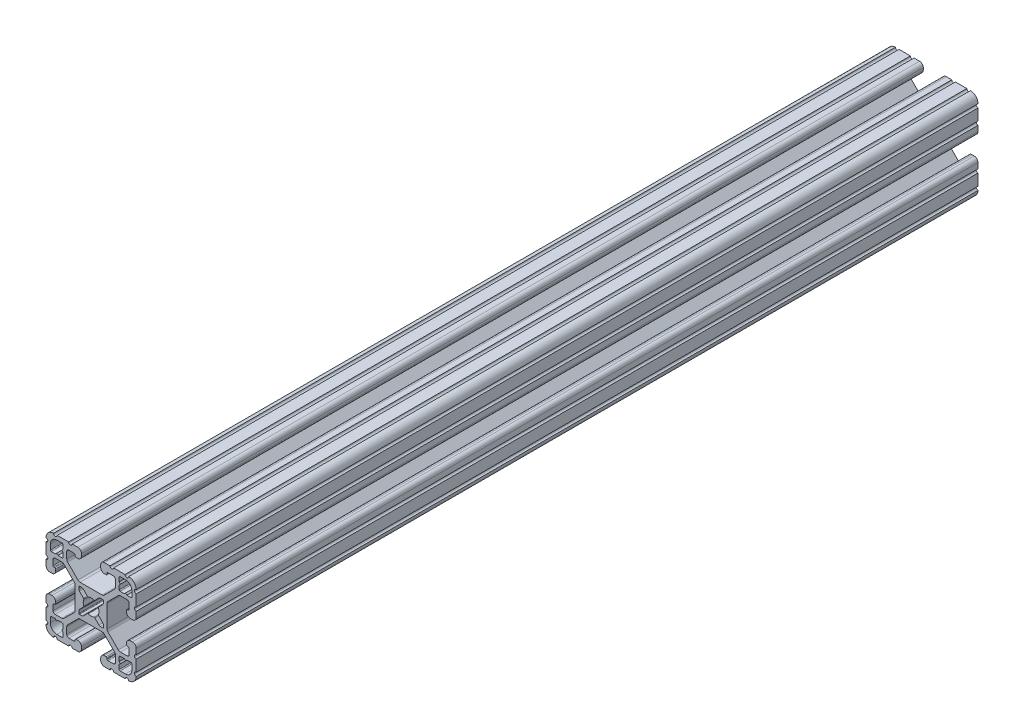
SolidWorks part; units mm, degrees
ref_plane "Front Plane" through (0, 0, 0) normal (0, 0, 1) x (1, 0, 0)
ref_plane "Top Plane" through (0, 0, 0) normal (0, 1, 0) x (1, 0, 0)
ref_plane "Right Plane" through (0, 0, 0) normal (1, 0, 0) x (0, 0, -1)
ref_plane "Plane1" through (0, 0, -2322.576) normal (0, 0, -1) x (-1, 0, 0)
sketch "Sketch1" plane through (0, 0, -2322.576) normal (0, 0, -1) x (-1, 0, 0)
  line L0 (17.2466, 14.4526) -> (17.2466, 12.2428)
  line L1 (16.8656, 11.8618) -> (15.0927, 11.8618)
  line L2 (15.0927, 11.8618) -> (14.5542, 12.4003)
  line L3 (14.5542, 12.4003) -> (14.0157, 11.8618)
  line L4 (14.0157, 11.8618) -> (12.2428, 11.8618)
  line L5 (11.8618, 12.2428) -> (11.8618, 14.0157)
  line L6 (11.8618, 14.0157) -> (12.4003, 14.5542)
  line L7 (12.4003, 14.5542) -> (11.8618, 15.0927)
  line L8 (11.8618, 15.0927) -> (11.8618, 16.8656)
  line L9 (12.2428, 17.2466) -> (14.4526, 17.2466)
  line L10 (17.2466, -12.2428) -> (17.2466, -14.4526)
  line L11 (14.4526, -17.2466) -> (12.2428, -17.2466)
  line L12 (11.8618, -16.8656) -> (11.8618, -15.0927)
  line L13 (11.8618, -15.0927) -> (12.4003, -14.5542)
  line L14 (12.4003, -14.5542) -> (11.8618, -14.0157)
  line L15 (11.8618, -14.0157) -> (11.8618, -12.2428)
  line L16 (12.2428, -11.8618) -> (14.0157, -11.8618)
  line L17 (14.0157, -11.8618) -> (14.5542, -12.4003)
  line L18 (14.5542, -12.4003) -> (15.0927, -11.8618)
  line L19 (15.0927, -11.8618) -> (16.8656, -11.8618)
  line L20 (5.1689, -3.9207) -> (5.1689, -4.9149)
  line L21 (4.9149, -5.1689) -> (3.9207, -5.1689)
  line L22 (3.2921, -4.9085) -> (1.5823, -3.1988)
  line L23 (-1.5823, -3.1988) -> (-3.2921, -4.9085)
  line L24 (-3.9207, -5.1689) -> (-4.9149, -5.1689)
  line L25 (-5.1689, -4.9149) -> (-5.1689, -3.9207)
  line L26 (-4.9085, -3.2921) -> (-3.1988, -1.5823)
  line L27 (-3.1988, 1.5823) -> (-4.9085, 3.2921)
  line L28 (-5.1689, 3.9207) -> (-5.1689, 4.9149)
  line L29 (-4.9149, 5.1689) -> (-3.9207, 5.1689)
  line L30 (-3.2921, 4.9085) -> (-1.5823, 3.1988)
  line L31 (1.5823, 3.1988) -> (3.2921, 4.9085)
  line L32 (3.9207, 5.1689) -> (4.9149, 5.1689)
  line L33 (5.1689, 4.9149) -> (5.1689, 3.9207)
  line L34 (4.9085, 3.2921) -> (3.1988, 1.5823)
  line L35 (3.1988, -1.5823) -> (4.9085, -3.2921)
  line L36 (-11.8618, -12.2428) -> (-11.8618, -14.0157)
  line L37 (-11.8618, -14.0157) -> (-12.4003, -14.5542)
  line L38 (-12.4003, -14.5542) -> (-11.8618, -15.0927)
  line L39 (-11.8618, -15.0927) -> (-11.8618, -16.8656)
  line L40 (-12.2428, -17.2466) -> (-14.4526, -17.2466)
  line L41 (-17.2466, -14.4526) -> (-17.2466, -12.2428)
  line L42 (-16.8656, -11.8618) -> (-15.0927, -11.8618)
  line L43 (-15.0927, -11.8618) -> (-14.5542, -12.4003)
  line L44 (-14.5542, -12.4003) -> (-14.0157, -11.8618)
  line L45 (-14.0157, -11.8618) -> (-12.2428, -11.8618)
  line L46 (-11.8618, 16.8656) -> (-11.8618, 15.0927)
  line L47 (-11.8618, 15.0927) -> (-12.4003, 14.5542)
  line L48 (-12.4003, 14.5542) -> (-11.8618, 14.0157)
  line L49 (-11.8618, 14.0157) -> (-11.8618, 12.2428)
  line L50 (-12.2428, 11.8618) -> (-14.0157, 11.8618)
  line L51 (-14.0157, 11.8618) -> (-14.5542, 12.4003)
  line L52 (-14.5542, 12.4003) -> (-15.0927, 11.8618)
  line L53 (-15.0927, 11.8618) -> (-16.8656, 11.8618)
  line L54 (-17.2466, 12.2428) -> (-17.2466, 14.4526)
  line L55 (-14.4526, 17.2466) -> (-12.2428, 17.2466)
  line L56 (19.05, -14.3256) -> (19.05, -9.4996)
  line L57 (19.05, -7.9756) -> (19.05, -5.6388)
  line L58 (17.4752, -4.064) -> (16.5608, -4.064)
  line L59 (14.986, -5.6388) -> (14.986, -6.35)
  line L60 (15.367, -6.731) -> (15.6972, -6.731)
  line L61 (16.0782, -7.112) -> (16.0782, -9.398)
  line L62 (15.1892, -10.287) -> (12.3756, -10.287)
  line L63 (11.4776, -9.915) -> (7.1157, -5.5531)
  line L64 (6.7437, -4.6551) -> (6.7437, 4.6551)
  line L65 (7.1157, 5.5531) -> (11.4776, 9.915)
  line L66 (12.3756, 10.287) -> (15.1892, 10.287)
  line L67 (16.0782, 9.398) -> (16.0782, 7.112)
  line L68 (15.6972, 6.731) -> (15.367, 6.731)
  line L69 (14.986, 6.35) -> (14.986, 5.6388)
  line L70 (16.5608, 4.064) -> (17.4752, 4.064)
  line L71 (19.05, 5.6388) -> (19.05, 7.9756)
  line L72 (19.05, 9.4996) -> (19.05, 14.3256)
  line L73 (14.3256, 19.05) -> (9.4996, 19.05)
  line L74 (7.9756, 19.05) -> (5.6388, 19.05)
  line L75 (4.064, 17.4752) -> (4.064, 16.5608)
  line L76 (5.6388, 14.986) -> (6.35, 14.986)
  line L77 (6.731, 15.367) -> (6.731, 15.6972)
  line L78 (7.112, 16.0782) -> (9.398, 16.0782)
  line L79 (10.287, 15.1892) -> (10.287, 12.3756)
  line L80 (9.915, 11.4776) -> (5.5531, 7.1157)
  line L81 (4.6551, 6.7437) -> (-4.6551, 6.7437)
  line L82 (-5.5531, 7.1157) -> (-9.915, 11.4776)
  line L83 (-10.287, 12.3756) -> (-10.287, 15.1892)
  line L84 (-9.398, 16.0782) -> (-7.112, 16.0782)
  line L85 (-6.731, 15.6972) -> (-6.731, 15.367)
  line L86 (-6.35, 14.986) -> (-5.6388, 14.986)
  line L87 (-4.064, 16.5608) -> (-4.064, 17.4752)
  line L88 (-5.6388, 19.05) -> (-7.9756, 19.05)
  line L89 (-9.4996, 19.05) -> (-14.3256, 19.05)
  line L90 (-19.05, 14.3256) -> (-19.05, 9.4996)
  line L91 (-19.05, 7.9756) -> (-19.05, 5.6388)
  line L92 (-17.4752, 4.064) -> (-16.5608, 4.064)
  line L93 (-14.986, 5.6388) -> (-14.986, 6.35)
  line L94 (-15.367, 6.731) -> (-15.6972, 6.731)
  line L95 (-16.0782, 7.112) -> (-16.0782, 9.398)
  line L96 (-15.1892, 10.287) -> (-12.3756, 10.287)
  line L97 (-11.4776, 9.915) -> (-7.1157, 5.5531)
  line L98 (-6.7437, 4.6551) -> (-6.7437, -4.6551)
  line L99 (-7.1157, -5.5531) -> (-11.4776, -9.915)
  line L100 (-12.3756, -10.287) -> (-15.1892, -10.287)
  line L101 (-16.0782, -9.398) -> (-16.0782, -7.112)
  line L102 (-15.6972, -6.731) -> (-15.367, -6.731)
  line L103 (-14.986, -6.35) -> (-14.986, -5.6388)
  line L104 (-16.5608, -4.064) -> (-17.4752, -4.064)
  line L105 (-19.05, -5.6388) -> (-19.05, -7.9756)
  line L106 (-19.05, -9.4996) -> (-19.05, -14.3256)
  line L107 (-14.3256, -19.05) -> (-9.4996, -19.05)
  line L108 (-7.9756, -19.05) -> (-5.6388, -19.05)
  line L109 (-4.064, -17.4752) -> (-4.064, -16.5608)
  line L110 (-5.6388, -14.986) -> (-6.35, -14.986)
  line L111 (-6.731, -15.367) -> (-6.731, -15.6972)
  line L112 (-7.112, -16.0782) -> (-9.398, -16.0782)
  line L113 (-10.287, -15.1892) -> (-10.287, -12.3756)
  line L114 (-9.915, -11.4776) -> (-5.5531, -7.1157)
  line L115 (-4.6551, -6.7437) -> (4.6551, -6.7437)
  line L116 (5.5531, -7.1157) -> (9.915, -11.4776)
  line L117 (10.287, -12.3756) -> (10.287, -15.1892)
  line L118 (9.398, -16.0782) -> (7.112, -16.0782)
  line L119 (6.731, -15.6972) -> (6.731, -15.367)
  line L120 (6.35, -14.986) -> (5.6388, -14.986)
  line L121 (4.064, -16.5608) -> (4.064, -17.4752)
  line L122 (5.6388, -19.05) -> (7.9756, -19.05)
  line L123 (9.4996, -19.05) -> (14.3256, -19.05)
  arc A0 (17.2466, 12.2428) -> (16.8656, 11.8618) centre (16.8656, 12.2428) cw
  arc A1 (12.2428, 11.8618) -> (11.8618, 12.2428) centre (12.2428, 12.2428) cw
  arc A2 (11.8618, 16.8656) -> (12.2428, 17.2466) centre (12.2428, 16.8656) cw
  arc A3 (14.4526, 17.2466) -> (17.2466, 14.4526) centre (14.4526, 14.4526) cw
  arc A4 (17.2466, -14.4526) -> (14.4526, -17.2466) centre (14.4526, -14.4526) cw
  arc A5 (12.2428, -17.2466) -> (11.8618, -16.8656) centre (12.2428, -16.8656) cw
  arc A6 (11.8618, -12.2428) -> (12.2428, -11.8618) centre (12.2428, -12.2428) cw
  arc A7 (16.8656, -11.8618) -> (17.2466, -12.2428) centre (16.8656, -12.2428) cw
  arc A8 (5.1689, -4.9149) -> (4.9149, -5.1689) centre (4.9149, -4.9149) cw
  arc A9 (3.9207, -5.1689) -> (3.2921, -4.9085) centre (3.9207, -4.2799) cw
  arc A10 (1.5823, -3.1988) -> (1.178, -3.1119) centre (1.3129, -3.4682) ccw
  arc A11 (1.178, -3.1119) -> (-1.178, -3.1119) centre (0, 0) cw
  arc A12 (-1.178, -3.1119) -> (-1.5823, -3.1988) centre (-1.3129, -3.4682) ccw
  arc A13 (-3.2921, -4.9085) -> (-3.9207, -5.1689) centre (-3.9207, -4.2799) cw
  arc A14 (-4.9149, -5.1689) -> (-5.1689, -4.9149) centre (-4.9149, -4.9149) cw
  arc A15 (-5.1689, -3.9207) -> (-4.9085, -3.2921) centre (-4.2799, -3.9207) cw
  arc A16 (-3.1988, -1.5823) -> (-3.1119, -1.178) centre (-3.4682, -1.3129) ccw
  arc A17 (-3.1119, -1.178) -> (-3.1119, 1.178) centre (0, 0) cw
  arc A18 (-3.1119, 1.178) -> (-3.1988, 1.5823) centre (-3.4682, 1.3129) ccw
  arc A19 (-4.9085, 3.2921) -> (-5.1689, 3.9207) centre (-4.2799, 3.9207) cw
  arc A20 (-5.1689, 4.9149) -> (-4.9149, 5.1689) centre (-4.9149, 4.9149) cw
  arc A21 (-3.9207, 5.1689) -> (-3.2921, 4.9085) centre (-3.9207, 4.2799) cw
  arc A22 (-1.5823, 3.1988) -> (-1.178, 3.1119) centre (-1.3129, 3.4682) ccw
  arc A23 (-1.178, 3.1119) -> (1.178, 3.1119) centre (0, 0) cw
  arc A24 (1.178, 3.1119) -> (1.5823, 3.1988) centre (1.3129, 3.4682) ccw
  arc A25 (3.2921, 4.9085) -> (3.9207, 5.1689) centre (3.9207, 4.2799) cw
  arc A26 (4.9149, 5.1689) -> (5.1689, 4.9149) centre (4.9149, 4.9149) cw
  arc A27 (5.1689, 3.9207) -> (4.9085, 3.2921) centre (4.2799, 3.9207) cw
  arc A28 (3.1988, 1.5823) -> (3.1119, 1.178) centre (3.4682, 1.3129) ccw
  arc A29 (3.1119, 1.178) -> (3.1119, -1.178) centre (0, 0) cw
  arc A30 (3.1119, -1.178) -> (3.1988, -1.5823) centre (3.4682, -1.3129) ccw
  arc A31 (4.9085, -3.2921) -> (5.1689, -3.9207) centre (4.2799, -3.9207) cw
  arc A32 (-11.8618, -16.8656) -> (-12.2428, -17.2466) centre (-12.2428, -16.8656) cw
  arc A33 (-14.4526, -17.2466) -> (-17.2466, -14.4526) centre (-14.4526, -14.4526) cw
  arc A34 (-17.2466, -12.2428) -> (-16.8656, -11.8618) centre (-16.8656, -12.2428) cw
  arc A35 (-12.2428, -11.8618) -> (-11.8618, -12.2428) centre (-12.2428, -12.2428) cw
  arc A36 (-12.2428, 17.2466) -> (-11.8618, 16.8656) centre (-12.2428, 16.8656) cw
  arc A37 (-11.8618, 12.2428) -> (-12.2428, 11.8618) centre (-12.2428, 12.2428) cw
  arc A38 (-16.8656, 11.8618) -> (-17.2466, 12.2428) centre (-16.8656, 12.2428) cw
  arc A39 (-17.2466, 14.4526) -> (-14.4526, 17.2466) centre (-14.4526, 14.4526) cw
  arc A40 (19.05, -9.4996) -> (19.05, -7.9756) centre (19.05, -8.7376) cw
  arc A41 (19.05, -5.6388) -> (17.4752, -4.064) centre (17.4752, -5.6388) ccw
  arc A42 (16.5608, -4.064) -> (14.986, -5.6388) centre (16.5608, -5.6388) ccw
  arc A43 (14.986, -6.35) -> (15.367, -6.731) centre (15.367, -6.35) ccw
  arc A44 (15.6972, -6.731) -> (16.0782, -7.112) centre (15.6972, -7.112) cw
  arc A45 (16.0782, -9.398) -> (15.1892, -10.287) centre (15.1892, -9.398) cw
  arc A46 (12.3756, -10.287) -> (11.4776, -9.915) centre (12.3756, -9.017) cw
  arc A47 (7.1157, -5.5531) -> (6.7437, -4.6551) centre (8.0137, -4.6551) cw
  arc A48 (6.7437, 4.6551) -> (7.1157, 5.5531) centre (8.0137, 4.6551) cw
  arc A49 (11.4776, 9.915) -> (12.3756, 10.287) centre (12.3756, 9.017) cw
  arc A50 (15.1892, 10.287) -> (16.0782, 9.398) centre (15.1892, 9.398) cw
  arc A51 (16.0782, 7.112) -> (15.6972, 6.731) centre (15.6972, 7.112) cw
  arc A52 (15.367, 6.731) -> (14.986, 6.35) centre (15.367, 6.35) ccw
  arc A53 (14.986, 5.6388) -> (16.5608, 4.064) centre (16.5608, 5.6388) ccw
  arc A54 (17.4752, 4.064) -> (19.05, 5.6388) centre (17.4752, 5.6388) ccw
  arc A55 (19.05, 7.9756) -> (19.05, 9.4996) centre (19.05, 8.7376) cw
  arc A56 (19.05, 14.3256) -> (19.0499, 15.8496) centre (19.05, 15.0876) cw
  arc A57 (19.0499, 15.8496) -> (15.8496, 19.0499) centre (15.875, 15.875) ccw
  arc A58 (15.8496, 19.0499) -> (14.3256, 19.05) centre (15.0876, 19.05) cw
  arc A59 (9.4996, 19.05) -> (7.9756, 19.05) centre (8.7376, 19.05) cw
  arc A60 (5.6388, 19.05) -> (4.064, 17.4752) centre (5.6388, 17.4752) ccw
  arc A61 (4.064, 16.5608) -> (5.6388, 14.986) centre (5.6388, 16.5608) ccw
  arc A62 (6.35, 14.986) -> (6.731, 15.367) centre (6.35, 15.367) ccw
  arc A63 (6.731, 15.6972) -> (7.112, 16.0782) centre (7.112, 15.6972) cw
  arc A64 (9.398, 16.0782) -> (10.287, 15.1892) centre (9.398, 15.1892) cw
  arc A65 (10.287, 12.3756) -> (9.915, 11.4776) centre (9.017, 12.3756) cw
  arc A66 (5.5531, 7.1157) -> (4.6551, 6.7437) centre (4.6551, 8.0137) cw
  arc A67 (-4.6551, 6.7437) -> (-5.5531, 7.1157) centre (-4.6551, 8.0137) cw
  arc A68 (-9.915, 11.4776) -> (-10.287, 12.3756) centre (-9.017, 12.3756) cw
  arc A69 (-10.287, 15.1892) -> (-9.398, 16.0782) centre (-9.398, 15.1892) cw
  arc A70 (-7.112, 16.0782) -> (-6.731, 15.6972) centre (-7.112, 15.6972) cw
  arc A71 (-6.731, 15.367) -> (-6.35, 14.986) centre (-6.35, 15.367) ccw
  arc A72 (-5.6388, 14.986) -> (-4.064, 16.5608) centre (-5.6388, 16.5608) ccw
  arc A73 (-4.064, 17.4752) -> (-5.6388, 19.05) centre (-5.6388, 17.4752) ccw
  arc A74 (-7.9756, 19.05) -> (-9.4996, 19.05) centre (-8.7376, 19.05) cw
  arc A75 (-14.3256, 19.05) -> (-15.8496, 19.0499) centre (-15.0876, 19.05) cw
  arc A76 (-15.8496, 19.0499) -> (-19.0499, 15.8496) centre (-15.875, 15.875) ccw
  arc A77 (-19.0499, 15.8496) -> (-19.05, 14.3256) centre (-19.05, 15.0876) cw
  arc A78 (-19.05, 9.4996) -> (-19.05, 7.9756) centre (-19.05, 8.7376) cw
  arc A79 (-19.05, 5.6388) -> (-17.4752, 4.064) centre (-17.4752, 5.6388) ccw
  arc A80 (-16.5608, 4.064) -> (-14.986, 5.6388) centre (-16.5608, 5.6388) ccw
  arc A81 (-14.986, 6.35) -> (-15.367, 6.731) centre (-15.367, 6.35) ccw
  arc A82 (-15.6972, 6.731) -> (-16.0782, 7.112) centre (-15.6972, 7.112) cw
  arc A83 (-16.0782, 9.398) -> (-15.1892, 10.287) centre (-15.1892, 9.398) cw
  arc A84 (-12.3756, 10.287) -> (-11.4776, 9.915) centre (-12.3756, 9.017) cw
  arc A85 (-7.1157, 5.5531) -> (-6.7437, 4.6551) centre (-8.0137, 4.6551) cw
  arc A86 (-6.7437, -4.6551) -> (-7.1157, -5.5531) centre (-8.0137, -4.6551) cw
  arc A87 (-11.4776, -9.915) -> (-12.3756, -10.287) centre (-12.3756, -9.017) cw
  arc A88 (-15.1892, -10.287) -> (-16.0782, -9.398) centre (-15.1892, -9.398) cw
  arc A89 (-16.0782, -7.112) -> (-15.6972, -6.731) centre (-15.6972, -7.112) cw
  arc A90 (-15.367, -6.731) -> (-14.986, -6.35) centre (-15.367, -6.35) ccw
  arc A91 (-14.986, -5.6388) -> (-16.5608, -4.064) centre (-16.5608, -5.6388) ccw
  arc A92 (-17.4752, -4.064) -> (-19.05, -5.6388) centre (-17.4752, -5.6388) ccw
  arc A93 (-19.05, -7.9756) -> (-19.05, -9.4996) centre (-19.05, -8.7376) cw
  arc A94 (-19.05, -14.3256) -> (-19.0499, -15.8496) centre (-19.05, -15.0876) cw
  arc A95 (-19.0499, -15.8496) -> (-15.8496, -19.0499) centre (-15.875, -15.875) ccw
  arc A96 (-15.8496, -19.0499) -> (-14.3256, -19.05) centre (-15.0876, -19.05) cw
  arc A97 (-9.4996, -19.05) -> (-7.9756, -19.05) centre (-8.7376, -19.05) cw
  arc A98 (-5.6388, -19.05) -> (-4.064, -17.4752) centre (-5.6388, -17.4752) ccw
  arc A99 (-4.064, -16.5608) -> (-5.6388, -14.986) centre (-5.6388, -16.5608) ccw
  arc A100 (-6.35, -14.986) -> (-6.731, -15.367) centre (-6.35, -15.367) ccw
  arc A101 (-6.731, -15.6972) -> (-7.112, -16.0782) centre (-7.112, -15.6972) cw
  arc A102 (-9.398, -16.0782) -> (-10.287, -15.1892) centre (-9.398, -15.1892) cw
  arc A103 (-10.287, -12.3756) -> (-9.915, -11.4776) centre (-9.017, -12.3756) cw
  arc A104 (-5.5531, -7.1157) -> (-4.6551, -6.7437) centre (-4.6551, -8.0137) cw
  arc A105 (4.6551, -6.7437) -> (5.5531, -7.1157) centre (4.6551, -8.0137) cw
  arc A106 (9.915, -11.4776) -> (10.287, -12.3756) centre (9.017, -12.3756) cw
  arc A107 (10.287, -15.1892) -> (9.398, -16.0782) centre (9.398, -15.1892) cw
  arc A108 (7.112, -16.0782) -> (6.731, -15.6972) centre (7.112, -15.6972) cw
  arc A109 (6.731, -15.367) -> (6.35, -14.986) centre (6.35, -15.367) ccw
  arc A110 (5.6388, -14.986) -> (4.064, -16.5608) centre (5.6388, -16.5608) ccw
  arc A111 (4.064, -17.4752) -> (5.6388, -19.05) centre (5.6388, -17.4752) ccw
  arc A112 (7.9756, -19.05) -> (9.4996, -19.05) centre (8.7376, -19.05) cw
  arc A113 (14.3256, -19.05) -> (15.8496, -19.0499) centre (15.0876, -19.05) cw
  arc A114 (15.8496, -19.0499) -> (19.0499, -15.8496) centre (15.875, -15.875) ccw
  arc A115 (19.0499, -15.8496) -> (19.05, -14.3256) centre (19.05, -15.0876) cw
extrude "Boss-Extrude1" add sketch "Sketch1" against normal blind 355.6
